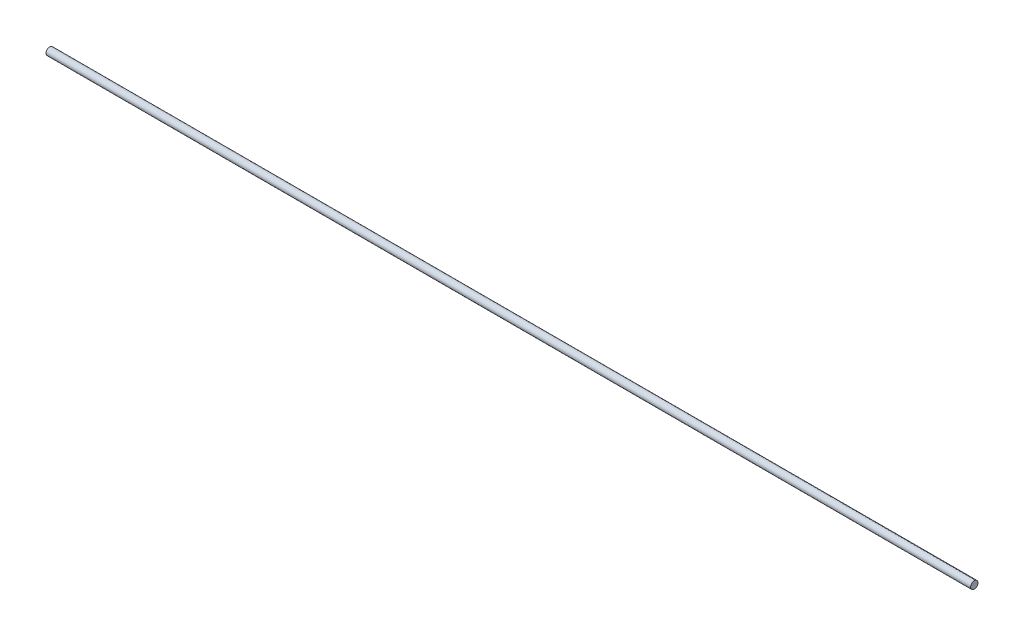
SolidWorks part; units mm, degrees
ref_plane "Plan de face" through (0, 0, 0) normal (0, 0, 1) x (1, 0, 0)
ref_plane "Plan de dessus" through (0, 0, 0) normal (0, 1, 0) x (1, 0, 0)
ref_plane "Plan de droite" through (0, 0, 0) normal (1, 0, 0) x (0, 0, -1)
sketch "Esquisse1" plane through (0, 0, 0) normal (1, 0, 0) x (0, 0, -1)
  circle A0 centre (0, 0) radius 2
extrude "Extrusion1" add sketch "Esquisse1" along normal blind 500
